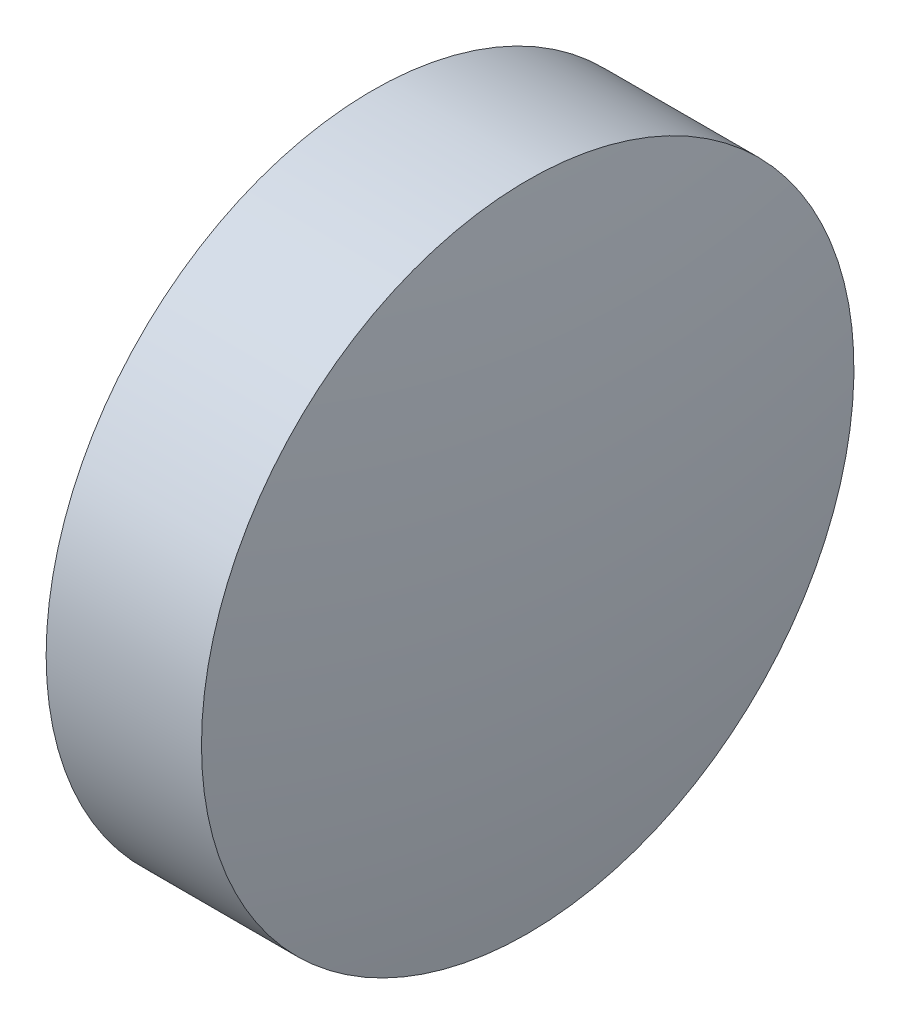
SolidWorks part; units mm, degrees
ref_plane "前视基准面" through (0, 0, 0) normal (0, 0, 1) x (1, 0, 0)
ref_plane "上视基准面" through (0, 0, 0) normal (0, 1, 0) x (1, 0, 0)
ref_plane "右视基准面" through (0, 0, 0) normal (1, 0, 0) x (0, 0, -1)
sketch "草图2" plane through (0, 0, 0) normal (0, 0, 1) x (1, 0, 0)
  line L0 (443.4238, 32.7415) -> (448.8188, 32.7415) construction
  line L1 (444.2844, 32.7415) -> (444.2844, 35.8915)
  line L2 (444.2844, 35.8915) -> (445.7844, 35.8915)
  line L3 (446.0544, 32.7415) -> (444.2844, 32.7415)
  arc A0 (446.0544, 32.7415) -> (445.7844, 35.8915) centre (427.5444, 32.7415) ccw
revolve "旋转2" add sketch "草图2" angle 360 about L0
